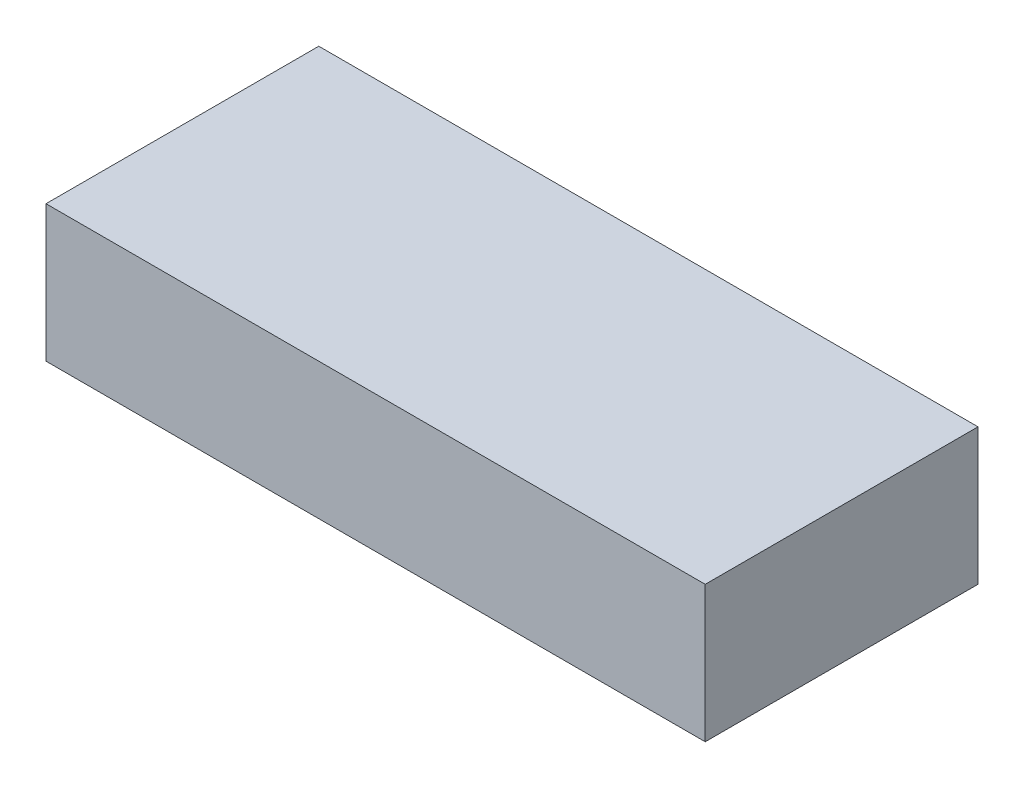
SolidWorks part; units mm, degrees
material "Pine"
ref_plane "Front Plane" through (0, 0, 0) normal (0, 0, 1) x (1, 0, 0)
ref_plane "Top Plane" through (0, 0, 0) normal (0, 1, 0) x (1, 0, 0)
ref_plane "Right Plane" through (0, 0, 0) normal (1, 0, 0) x (0, 0, -1)
sketch "Sketch1" plane through (0, 0, 0) normal (0, 1, 0) x (1, 0, 0)
  line L1 (0, 0) -> (92.075, 0)
  line L2 (0, 0) -> (0, 38.1)
  line L3 (0, 38.1) -> (92.075, 38.1)
  line L4 (92.075, 0) -> (92.075, 38.1)
  dimension "D1" = 38.1
  dimension "D2" = 92.075
extrude "Boss-Extrude1" add sketch "Sketch1" along normal blind 19.05
